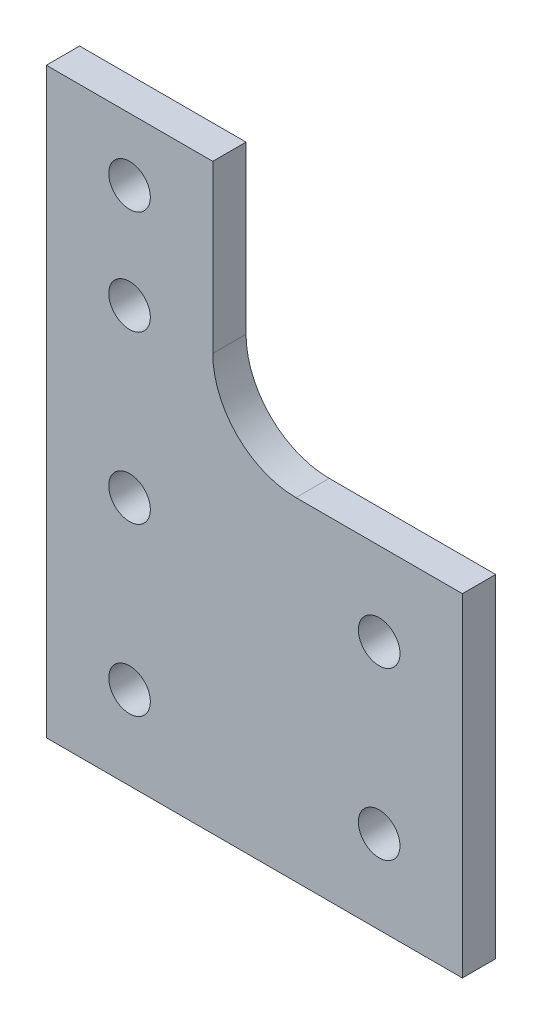
SolidWorks part; units mm, degrees
ref_plane "Front Plane" through (0, 0, 0) normal (0, 0, 1) x (1, 0, 0)
ref_plane "Top Plane" through (0, 0, 0) normal (0, 1, 0) x (1, 0, 0)
ref_plane "Right Plane" through (0, 0, 0) normal (1, 0, 0) x (0, 0, -1)
sketch "Sketch1" plane through (0, 0, 0) normal (0, 0, 1) x (1, 0, 0)
  line L0 (-20, -30) -> (-20, 40)
  line L1 (-20, -30) -> (30, -30)
  line L3 (-20, 40) -> (0, 40)
  line L4 (30, -30) -> (30, 10)
  line L5 (30, 10) -> (10, 10)
  line L8 (0, 40) -> (0, 20)
  circle A0 centre (-10, 32.5) radius 2.5
  circle A1 centre (-10, 0) radius 2.5
  circle A2 centre (-10, -20) radius 2.5
  circle A3 centre (20, 0) radius 2.5
  circle A4 centre (20, -20) radius 2.5
  circle A7 centre (-10, 20) radius 2.5
  arc A8 (10, 10) -> (0, 20) centre (10, 20) cw
  dimension "D4" = 10
  dimension "D5" = 20
  dimension "D6" = 10
  dimension "D7" = 10
  dimension "D8" = 5
  dimension "D9" = 5
  dimension "D12" = 10
  dimension "D13" = 5
  dimension "D14" = 10
  dimension "D15" = 5
  dimension "D18" = 5
  dimension "D19" = 7.5
  dimension "D20" = 5
  dimension "D21" = 12.5
  dimension "D11" = 10
  dimension "D24" = 20
  dimension "D25" = 10
  dimension "D26" = 20
  dimension "D28" = 10
  dimension "D29" = 10
  dimension "D22" = 30
  dimension "D23" = 30
  dimension "D32" = 20
  dimension "D33" = 70
  dimension "D34" = 30
extrude "Boss-Extrude1" add sketch "Sketch1" along normal blind 4
